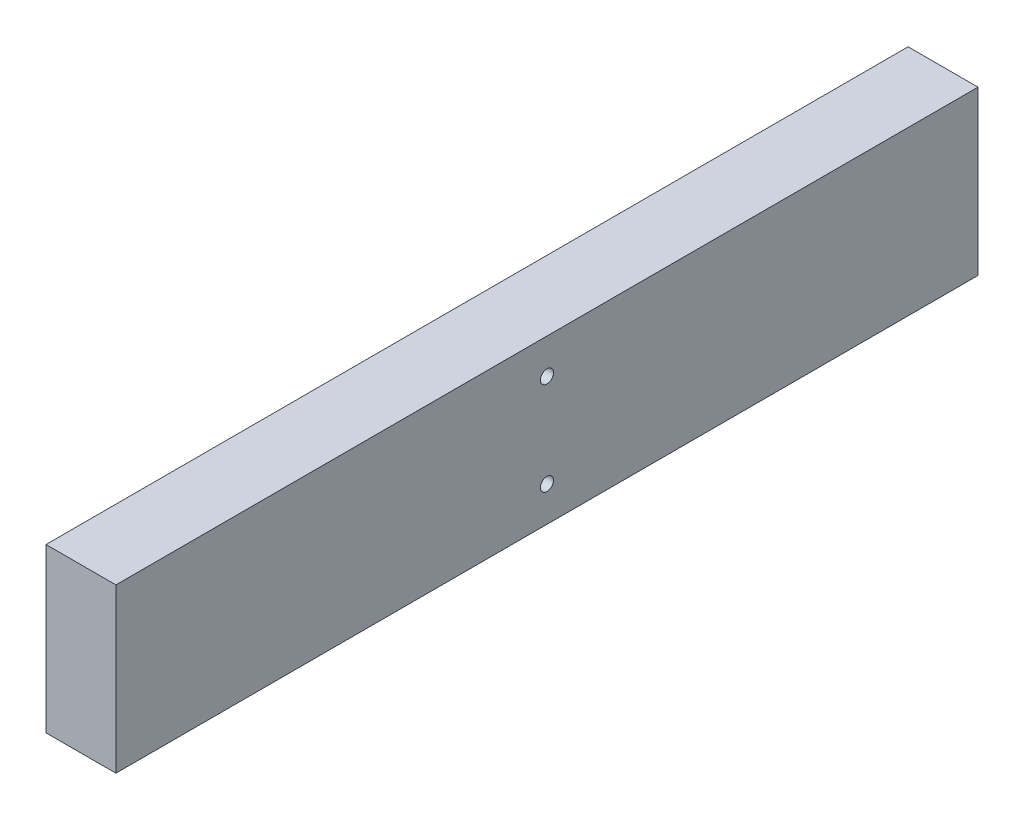
SolidWorks part; units mm, degrees
material "Pine"
ref_plane "Front Plane" through (0, 0, 0) normal (0, 0, 1) x (1, 0, 0)
ref_plane "Top Plane" through (0, 0, 0) normal (0, 1, 0) x (1, 0, 0)
ref_plane "Right Plane" through (0, 0, 0) normal (1, 0, 0) x (0, 0, -1)
sketch "Sketch1" plane through (0, 0, 0) normal (0, 0, 1) x (1, 0, 0)
  line L1 (-19.05, -44.45) -> (19.05, -44.45)
  line L2 (-19.05, -44.45) -> (-19.05, 44.45)
  line L3 (-19.05, 44.45) -> (19.05, 44.45)
  line L4 (19.05, -44.45) -> (19.05, 44.45)
  line L5 (-19.05, -44.45) -> (19.05, 44.45) construction
  line L6 (-19.05, 44.45) -> (19.05, -44.45) construction
  point P0 (0, 0)
  dimension "D1" = 88.9
  dimension "D2" = 38.1
extrude "Boss-Extrude1" add sketch "Sketch1" along normal blind 469.9
sketch "Sketch2" plane through (19.05, 0, 0) normal (1, 0, 0) x (0, 0, -1)
  line L1 (0, -44.45) -> (0, 44.45) construction
  line L2 (-234.95, 25.4) -> (-234.95, 44.45) construction
  line L5 (-234.95, -25.4) -> (-234.95, -44.45) construction
  line L8 (-469.9, 44.45) -> (0, 44.45) construction
  line L9 (-469.9, -44.45) -> (0, -44.45) construction
  point P0 (-234.95, 25.4)
  point P1 (-234.95, -25.4)
  point P8 (0, 0)
  point P11 (0, 0)
  point P14 (-234.95, -18.7275)
  point P15 (-234.95, 18.7261)
  dimension "D1" = 50.8
  dimension "D3" = 234.95
hole_wizard "9/32 (0.28125) Diameter Hole1" positions "Sketch3" profile "Sketch4" hole size "9/32" standard "ANSI Inch" end condition through all
sketch "Sketch3" plane through (19.05, 0, 0) normal (1, 0, 0) x (0, 0, -1)
  point P0 (-234.95, 25.4)
  point P3 (-234.95, -25.4)
sketch "Sketch4" plane through (19.05, 25.4, 234.95) normal (0, 1, 0) x (0, 0, -1)
  line L0 (0, 0) -> (0, 38.1)
  line L1 (0, 38.1) -> (3.5719, 38.1)
  line L2 (3.5719, 38.1) -> (3.5719, 0)
  line L5 (3.5719, 0) -> (0, 0)
  line L11 (0, -6.35) -> (0, 107.95) construction
  dimension "Thru Hole Dia." = 7.1437
  dimension "Thru Hole Depth" = 38.1
